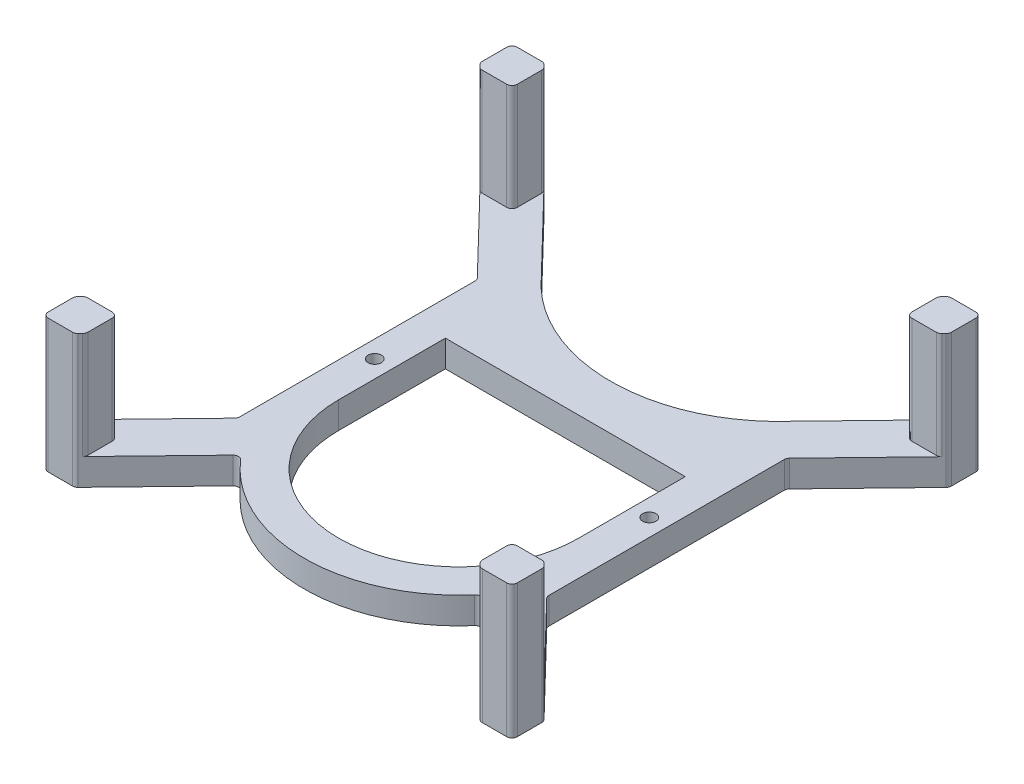
SolidWorks part; units mm, degrees
ref_plane "Front Plane" through (0, 0, 0) normal (0, 0, 1) x (1, 0, 0)
ref_plane "Top Plane" through (0, 0, 0) normal (0, 1, 0) x (1, 0, 0)
ref_plane "Right Plane" through (0, 0, 0) normal (1, 0, 0) x (0, 0, -1)
sketch "Sketch1" plane through (0, 0, 0) normal (0, 1, 0) x (1, 0, 0)
  line L0 (50, 60) -> (50, 40) construction
  line L1 (0, 0) -> (100, 0) construction
  line L2 (0, 0) -> (0, 100) construction
  line L3 (0, 100) -> (100, 100) construction
  line L4 (100, 0) -> (100, 100) construction
  line L5 (72.5, 60) -> (72.5, 40) construction
  line L6 (27.5, 60) -> (27.5, 40) construction
  line L7 (21, 27.9211) -> (21, 72.0789)
  line L8 (20.719, 72.7739) -> (6.281, 87.7093)
  line L9 (6, 88.4043) -> (6, 93)
  line L10 (7, 94) -> (11.5758, 94)
  line L11 (12.2948, 93.695) -> (26.5799, 78.9177)
  line L12 (27.3548, 78.1162) -> (50, 60) construction
  line L14 (0, 100) -> (27.3548, 78.1162) construction
  line L16 (0, 50) -> (100, 50) construction
  line L17 (50, 0) -> (50, 100) construction
  line L18 (27.5, 40) -> (27.5, 60)
  line L19 (72.6452, 78.1162) -> (50, 60) construction
  line L20 (72.5, 40) -> (72.5, 60)
  line L21 (87.7052, 93.695) -> (73.4201, 78.9177)
  line L22 (93, 94) -> (88.4242, 94)
  line L23 (94, 88.4043) -> (94, 93)
  line L24 (79.281, 72.7739) -> (93.719, 87.7093)
  line L25 (79, 27.9211) -> (79, 72.0789)
  line L26 (72.6452, 21.8838) -> (50, 40) construction
  line L27 (27.3548, 21.8838) -> (50, 40) construction
  line L28 (79.281, 27.2261) -> (93.719, 12.2907)
  line L29 (94, 11.5957) -> (94, 7)
  line L30 (93, 6) -> (88.4242, 6)
  line L31 (87.7052, 6.305) -> (73.4201, 21.0823)
  line L32 (12.2948, 6.305) -> (26.5799, 21.0823)
  line L33 (7, 6) -> (11.5758, 6)
  line L34 (6, 11.5957) -> (6, 7)
  line L35 (20.719, 27.2261) -> (6.281, 12.2907)
  line L36 (27.5, 60) -> (72.5, 60)
  arc A0 (72.5, 60) -> (27.5, 60) centre (50, 60) ccw construction
  arc A1 (27.5, 40) -> (72.5, 40) centre (50, 40) ccw construction
  arc A5 (21, 72.0789) -> (20.719, 72.7739) centre (20, 72.0789) ccw
  arc A6 (11.5758, 94) -> (12.2948, 93.695) centre (11.5758, 93) cw
  arc A7 (6, 93) -> (7, 94) centre (7, 93) cw
  arc A8 (6.281, 87.7093) -> (6, 88.4043) centre (7, 88.4043) cw
  arc A9 (93.719, 87.7093) -> (94, 88.4043) centre (93, 88.4043) ccw
  arc A10 (94, 93) -> (93, 94) centre (93, 93) ccw
  arc A11 (88.4242, 94) -> (87.7052, 93.695) centre (88.4242, 93) ccw
  arc A12 (79, 72.0789) -> (79.281, 72.7739) centre (80, 72.0789) cw
  arc A14 (71.9444, 21.041) -> (73.4201, 21.0823) centre (72.7011, 20.3872) cw
  arc A15 (79, 27.9211) -> (79.281, 27.2261) centre (80, 27.9211) ccw
  arc A16 (88.4242, 6) -> (87.7052, 6.305) centre (88.4242, 7) cw
  arc A17 (94, 7) -> (93, 6) centre (93, 7) cw
  arc A18 (93.719, 12.2907) -> (94, 11.5957) centre (93, 11.5957) cw
  arc A19 (6.281, 12.2907) -> (6, 11.5957) centre (7, 11.5957) ccw
  arc A20 (6, 7) -> (7, 6) centre (7, 7) ccw
  arc A21 (11.5758, 6) -> (12.2948, 6.305) centre (11.5758, 7) ccw
  arc A22 (21, 27.9211) -> (20.719, 27.2261) centre (20, 27.9211) cw
  arc A23 (28.0556, 21.041) -> (26.5799, 21.0823) centre (27.2989, 20.3872) ccw
  arc A24 (72.5, 40) -> (27.5, 40) centre (50, 40) cw
  arc A25 (28.0556, 21.041) -> (71.9444, 21.041) centre (50, 40) ccw
  arc A26 (26.5799, 78.9177) -> (73.4201, 78.9177) centre (50, 100) ccw
  point P7 (50, 50)
  point P12 (88, 6)
  point P20 (27.5, 50)
  point P24 (72.5, 50)
  point P25 (21, 50)
  point P35 (12, 94)
  point P38 (6, 94)
  point P41 (6, 88)
  point P58 (94, 88)
  point P59 (94, 94)
  point P60 (88, 94)
  point P96 (79, 50)
  point P97 (94, 6)
  point P98 (94, 12)
  point P99 (6, 12)
  point P100 (6, 6)
  point P101 (12, 6)
  dimension "D5" = 22.5
  dimension "D6" = 31.5113
  dimension "D1" = 100
  dimension "D2" = 100
  dimension "D3" = 50
  dimension "D4" = 50
  dimension "D7" = 6.5
  dimension "D8" = 180
  dimension "D9" = 6
  dimension "D10" = 6
  dimension "D11" = 6
  dimension "D12" = 6
  dimension "D13" = 20
extrude "Boss-Extrude1" add sketch "Sketch1" along normal blind 5
sketch "Sketch2" plane through (0, 5, 0) normal (0, 1, 0) x (1, 0, 0)
  line L0 (11.5758, 94) -> (7, 94) construction
  line L3 (11.5758, 94) -> (7, 94)
  line L4 (6, 88.4043) -> (6, 93)
  line L5 (6, 93) -> (6, 88.4043) construction
  line L6 (6.6719, 87.305) -> (6.281, 87.7093)
  line L7 (6.281, 87.7093) -> (20.719, 72.7739) construction
  line L8 (12.719, 93.2562) -> (12.2948, 93.695)
  line L9 (26.5799, 78.9177) -> (12.2948, 93.695) construction
  line L10 (7.3909, 87) -> (12, 87)
  line L11 (13, 88) -> (13, 92.5612)
  line L12 (21, 50) -> (79, 50) construction
  line L13 (21, 72.0789) -> (21, 27.9211) construction
  line L14 (79, 27.9211) -> (79, 72.0789) construction
  line L15 (50, 50) -> (50, 97.3435) construction
  line L16 (87, 88) -> (87, 92.5612)
  line L17 (92.6091, 87) -> (88, 87)
  line L18 (87.281, 93.2562) -> (87.7052, 93.695)
  line L19 (93.3281, 87.305) -> (93.719, 87.7093)
  line L20 (94, 88.4043) -> (94, 93)
  line L21 (88.4242, 94) -> (93, 94)
  line L22 (88.4242, 6) -> (93, 6)
  line L23 (94, 11.5957) -> (94, 7)
  line L24 (93.3281, 12.695) -> (93.719, 12.2907)
  line L25 (87.281, 6.7438) -> (87.7052, 6.305)
  line L26 (92.6091, 13) -> (88, 13)
  line L27 (87, 12) -> (87, 7.4388)
  line L28 (13, 12) -> (13, 7.4388)
  line L29 (7.3909, 13) -> (12, 13)
  line L30 (12.719, 6.7438) -> (12.2948, 6.305)
  line L31 (6.6719, 12.695) -> (6.281, 12.2907)
  line L32 (6, 11.5957) -> (6, 7)
  line L33 (11.5758, 6) -> (7, 6)
  arc A0 (7, 94) -> (6, 93) centre (7, 93) ccw
  arc A1 (6.281, 87.7093) -> (6, 88.4043) centre (7, 88.4043) cw
  arc A2 (11.5758, 94) -> (12.2948, 93.695) centre (11.5758, 93) cw
  arc A3 (6.6719, 87.305) -> (7.3909, 87) centre (7.3909, 88) ccw
  arc A4 (12.719, 93.2562) -> (13, 92.5612) centre (12, 92.5612) cw
  arc A5 (12, 87) -> (13, 88) centre (12, 88) ccw
  arc A6 (88, 87) -> (87, 88) centre (88, 88) cw
  arc A7 (87.281, 93.2562) -> (87, 92.5612) centre (88, 92.5612) ccw
  arc A8 (93.3281, 87.305) -> (92.6091, 87) centre (92.6091, 88) cw
  arc A9 (88.4242, 94) -> (87.7052, 93.695) centre (88.4242, 93) ccw
  arc A10 (93.719, 87.7093) -> (94, 88.4043) centre (93, 88.4043) ccw
  arc A11 (93, 94) -> (94, 93) centre (93, 93) cw
  arc A12 (93, 6) -> (94, 7) centre (93, 7) ccw
  arc A13 (93.719, 12.2907) -> (94, 11.5957) centre (93, 11.5957) cw
  arc A14 (88.4242, 6) -> (87.7052, 6.305) centre (88.4242, 7) cw
  arc A15 (93.3281, 12.695) -> (92.6091, 13) centre (92.6091, 12) ccw
  arc A16 (87.281, 6.7438) -> (87, 7.4388) centre (88, 7.4388) cw
  arc A17 (88, 13) -> (87, 12) centre (88, 12) ccw
  arc A18 (12, 13) -> (13, 12) centre (12, 12) cw
  arc A19 (12.719, 6.7438) -> (13, 7.4388) centre (12, 7.4388) ccw
  arc A20 (6.6719, 12.695) -> (7.3909, 13) centre (7.3909, 12) cw
  arc A21 (11.5758, 6) -> (12.2948, 6.305) centre (11.5758, 7) ccw
  arc A22 (6.281, 12.2907) -> (6, 11.5957) centre (7, 11.5957) ccw
  arc A23 (7, 6) -> (6, 7) centre (7, 7) cw
  point P19 (6.9667, 87)
  point P22 (13, 92.9655)
  point P54 (87, 92.9655)
  point P55 (93.0333, 87)
  point P92 (93.0333, 13)
  point P93 (87, 7.0345)
  point P94 (13, 7.0345)
  point P95 (6.9667, 13)
  dimension "D5" = 1
  dimension "D7" = 1
  dimension "D3" = 1
  dimension "D8" = 1
  dimension "D1" = 0
  dimension "D2" = 0
  dimension "D4" = 0
  dimension "D6" = 0
  dimension "D9" = 7
  dimension "D10" = 7
extrude "Boss-Extrude2" add sketch "Sketch2" along normal blind 20
sketch "Sketch3" plane through (0, 5, 0) normal (0, 1, 0) x (1, 0, 0)
  line L0 (21, 50) -> (79, 50) construction
  line L1 (21, 72.0789) -> (21, 27.9211) construction
  line L2 (79, 27.9211) -> (79, 72.0789) construction
  line L3 (50, 82.5) -> (50, 17.5) construction
  line L4 (27.5, 60) -> (27.5, 40) construction
  arc A0 (72.5, 60) -> (27.5, 60) centre (50, 60) ccw construction
  arc A1 (27.5, 40) -> (72.5, 40) centre (50, 40) ccw construction
  point P0 (24.25, 50)
  point P17 (75.75, 50)
  dimension "D1" = 0
  dimension "D2" = 3.25
hole_wizard "Tap Drill for M3x0.5 Tap1" positions "3DSketch1" profile "Sketch4" hole size "M3x0.5" standard "ANSI Metric"
sketch3d "3DSketch1"
  point P0 (24.25, 5, -50)
  point P3 (75.75, 5, -50)
sketch "Sketch4" plane through (24.25, 5, -50) normal (1, 0, 0) x (0, 0, 1)
  line L0 (0, 0) -> (0, 6.7511)
  line L1 (0, 6.7511) -> (1.25, 6)
  line L2 (1.25, 6) -> (1.25, 0)
  line L5 (1.25, 0) -> (0, 0)
  line L10 (0, 6.7511) -> (-1.25, 6) construction
  line L11 (0, -6.35) -> (0, 107.95) construction
  dimension "Hole Dia." = 2.5
  dimension "Hole Depth" = 6
  dimension "Drill Angle" = 118
sketch "Sketch5" plane through (0, 25, 0) normal (0, 1, 0) x (1, 0, 0)
  line L0 (6, 11.5957) -> (6, 7) construction
  line L1 (7, 6) -> (11.5758, 6) construction
  line L2 (50, 17.5) -> (50, 82.5) construction
  line L3 (27.5, 50) -> (72.5, 50) construction
  line L4 (27.5, 60) -> (27.5, 40) construction
  line L5 (72.5, 40) -> (72.5, 60) construction
  arc A0 (27.5, 40) -> (72.5, 40) centre (50, 40) ccw construction
  point P0 (9.5, 9.5)
  point P17 (90.5, 9.5)
  point P18 (90.5, 90.5)
  point P19 (9.5, 90.5)
  dimension "D1" = 3.5
  dimension "D2" = 3.5
hole_wizard "Tap Drill for M2x0.4 Tap1" positions "3DSketch2" profile "Sketch6" hole size "M2x0.4" standard "ANSI Metric"
sketch3d "3DSketch2"
  point P0 (9.5, 25, -9.5)
  point P3 (9.5, 25, -90.5)
  point P6 (90.5, 25, -90.5)
  point P9 (90.5, 25, -9.5)
sketch "Sketch6" plane through (9.5, 25, -9.5) normal (1, 0, 0) x (0, 0, 1)
  line L0 (0, 0) -> (0, 6.4807)
  line L1 (0, 6.4807) -> (0.8, 6)
  line L2 (0.8, 6) -> (0.8, 0)
  line L5 (0.8, 0) -> (0, 0)
  line L10 (0, 6.4807) -> (-0.8, 6) construction
  line L11 (0, -6.35) -> (0, 107.95) construction
  dimension "Hole Dia." = 1.6
  dimension "Hole Depth" = 6
  dimension "Drill Angle" = 118
